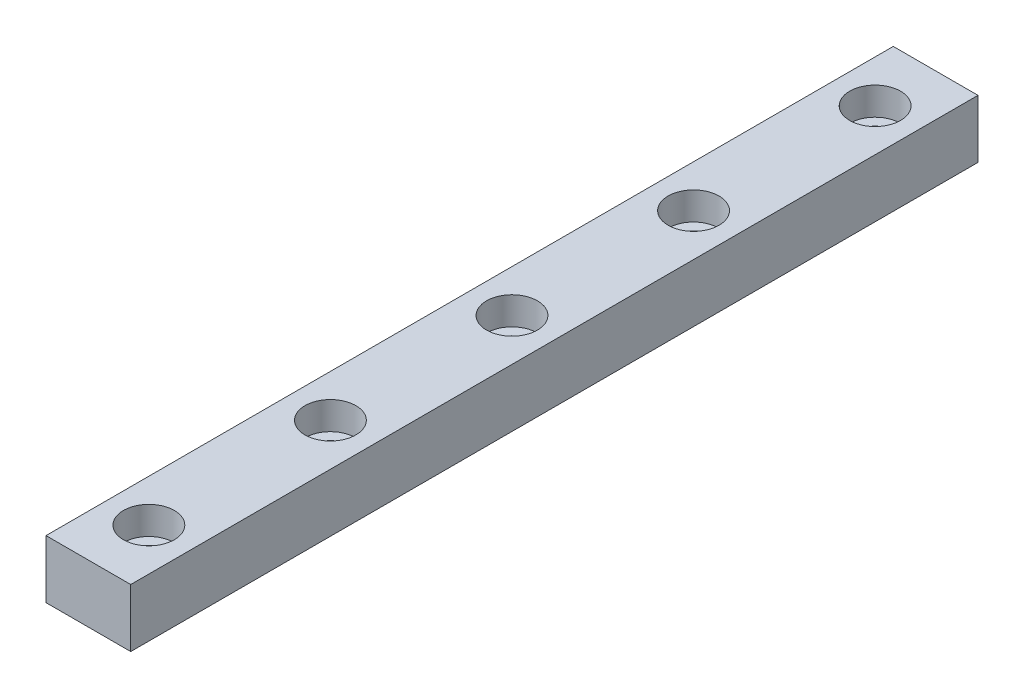
SolidWorks part; units mm, degrees
ref_plane "Front Plane" through (0, 0, 0) normal (0, 0, 1) x (1, 0, 0)
ref_plane "Top Plane" through (0, 0, 0) normal (0, 1, 0) x (1, 0, 0)
ref_plane "Right Plane" through (0, 0, 0) normal (1, 0, 0) x (0, 0, -1)
sketch "Sketch1" plane through (0, 0, 0) normal (0, 0, 1) x (1, 0, 0)
  line L1 (0, 0) -> (7, 0)
  line L2 (0, 0) -> (0, 4.8)
  line L3 (0, 4.8) -> (7, 4.8)
  line L4 (7, 0) -> (7, 4.8)
  dimension "D1" = 7
  dimension "D2" = 4.8
extrude "Boss-Extrude1" add sketch "Sketch1" along normal blind 70
hole_wizard "CBORE for M2 SHCS1" positions "Sketch2" profile "Sketch3" counterbore size "M2" standard "ANSI Metric" end condition through all
sketch "Sketch2" plane through (0, 4.8, 0) normal (0, 1, 0) x (1, 0, 0)
  line L0 (7, -70) -> (7, 0) construction
  line L1 (7, -70) -> (0, -70) construction
  point P0 (3.5, -65)
  point P14 (3.5, -50)
  point P15 (3.5, -35)
  point P16 (3.5, -20)
  point P17 (3.5, -5)
  dimension "D1" = 3.5
  dimension "D2" = 5
  dimension "D3" = 5
sketch "Sketch3" plane through (3.5, 4.8, 65) normal (1, 0, 0) x (0, 0, 1)
  line L0 (0, 0) -> (0, 4.8)
  line L1 (0, 4.8) -> (1.2, 4.8)
  line L3 (1.2, 4.8) -> (1.2, 2.3)
  line L4 (1.2, 2.3) -> (2.1, 2.3)
  line L5 (2.1, 2.3) -> (2.1, 0)
  line L7 (2.1, 0) -> (0, 0)
  line L11 (0, -6.35) -> (0, 107.95) construction
  dimension "Thru Hole Dia." = 2.4
  dimension "Thru Hole Depth" = 4.8
  dimension "C'Bore Dia." = 4.2
  dimension "C'Bore Depth" = 2.3
